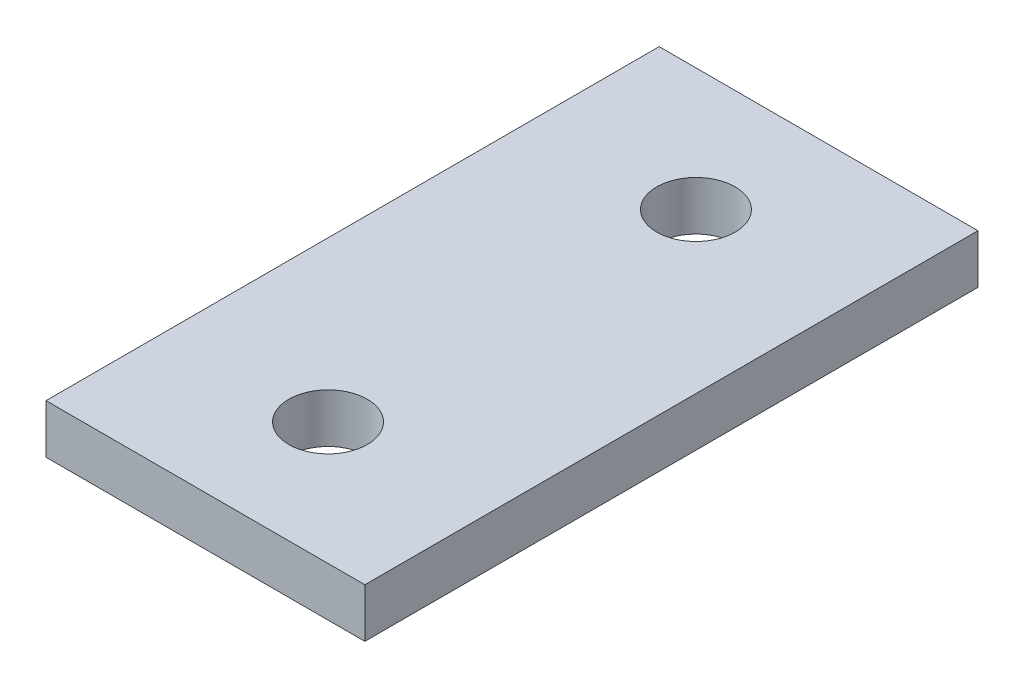
SolidWorks part; units mm, degrees
ref_plane "Front Plane" through (0, 0, 0) normal (0, 0, 1) x (1, 0, 0)
ref_plane "Top Plane" through (0, 0, 0) normal (0, 1, 0) x (1, 0, 0)
ref_plane "Right Plane" through (0, 0, 0) normal (1, 0, 0) x (0, 0, -1)
sketch "Sketch1" plane through (0, 0, 0) normal (0, 1, 0) x (1, 0, 0)
  line L0 (0, 12.5) -> (0, -12.5) construction
  line L1 (-6.5, -12.5) -> (6.5, -12.5)
  line L2 (-6.5, -12.5) -> (-6.5, 12.5)
  line L3 (-6.5, 12.5) -> (6.5, 12.5)
  line L4 (6.5, -12.5) -> (6.5, 12.5)
  line L5 (-6.5, -12.5) -> (6.5, 12.5) construction
  line L6 (-6.5, 12.5) -> (6.5, -12.5) construction
  circle A0 centre (0, 7.5) radius 1.6
  circle A1 centre (0, -7.5) radius 1.6
  point P0 (0, 0)
  dimension "D3" = 3.2
  dimension "D1" = 5
  dimension "D2" = 13
  dimension "D4" = 7.5
  dimension "D5" = 15
extrude "Boss-Extrude1" add sketch "Sketch1" along normal blind 2
